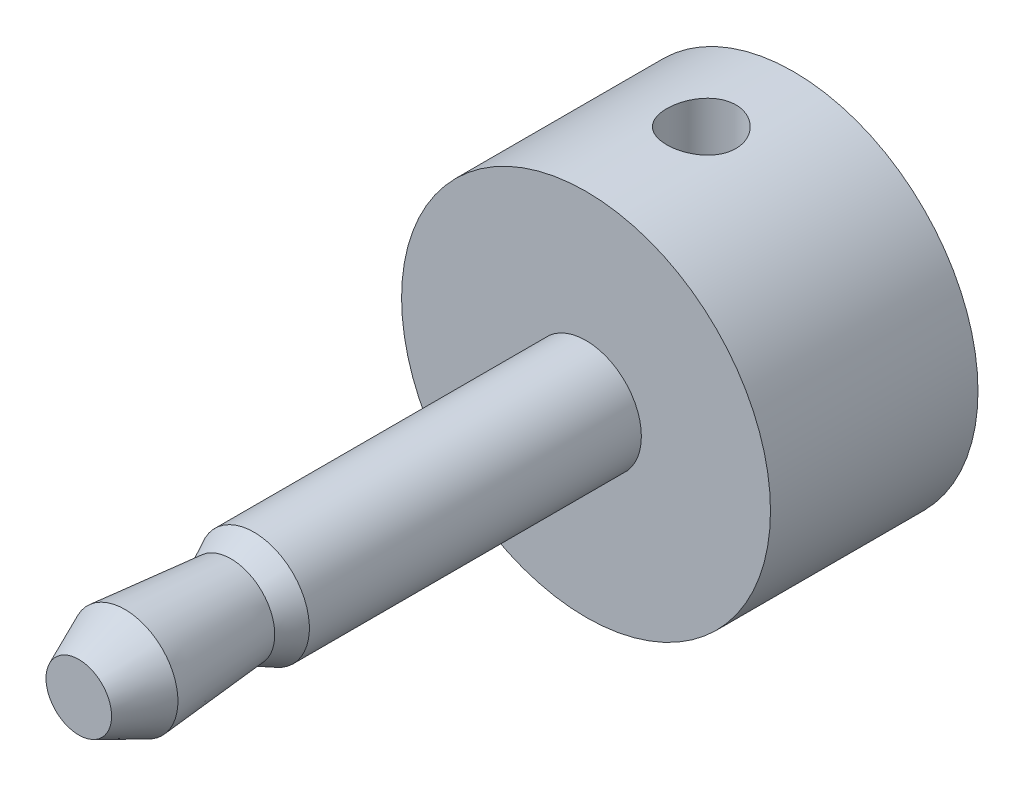
SolidWorks part; units mm, degrees
ref_plane "正面" through (0, 0, 0) normal (0, 0, 1) x (1, 0, 0)
ref_plane "平面" through (0, 0, 0) normal (0, 1, 0) x (1, 0, 0)
ref_plane "右側面" through (0, 0, 0) normal (1, 0, 0) x (0, 0, -1)
sketch "ｽｹｯﾁ1" plane through (0, 0, 0) normal (0, 0, 1) x (1, 0, 0)
  circle A0 centre (0, 0) radius 4
extrude "ﾎﾞｽ - 押し出し1" add sketch "ｽｹｯﾁ1" along normal blind 5.5
sketch "ｽｹｯﾁ2" plane through (0, 0, 5.5) normal (0, 0, 1) x (1, 0, 0)
  circle A0 centre (0, 0) radius 1.2
extrude "ﾎﾞｽ - 押し出し2" add sketch "ｽｹｯﾁ2" along normal blind 11
sketch "ｽｹｯﾁ3" plane through (0, 0, 16.5) normal (0, 0, 1) x (1, 0, 0)
  circle A0 centre (0, 0) radius 1.2 construction
  circle A1 centre (0, 0) radius 1.2 construction
  point P0 (-1.2, 0)
  point P1 (1.2, 0)
ref_plane "平面1" through (0, 0, 0) normal (0, 1, 0) x (1, 0, 0)
sketch "ｽｹｯﾁ4" plane through (0, 0, 0) normal (0, 1, 0) x (1, 0, 0)
  line L0 (1.2, -16.5) -> (0.7112, -16.5)
  line L5 (-1.2, -16.5) -> (1.2, -16.5) construction
  line L6 (0.7112, -16.5) -> (1.15, -15.5)
  line L7 (1.15, -15.5) -> (0.95, -13.2)
  line L8 (0.95, -13.2) -> (1.2, -12.7)
  line L9 (1.2, -16.5) -> (1.2, -5.5) construction
  line L10 (1.2, -12.7) -> (1.2, -16.5)
  point P12 (0, -16.5)
  dimension "D1" = 1
  dimension "D2" = 1.15
  dimension "D3" = 2.3
  dimension "D4" = 0.5
  dimension "D5" = 0.95
ref_axis "軸1" through (0, 0, 12.793) along (0, 0, 1)
revolve "ｶｯﾄ - 回転1" cut sketch "ｽｹｯﾁ4" angle 360 about axis through (0, 0, 12.793) along (0, 0, 1)
sketch "ｽｹｯﾁ6" plane through (0, 0, 0) normal (0, 1, 0) x (1, 0, 0)
  line L0 (4, 0) -> (-4, 0) construction
  circle A0 centre (0, -3) radius 0.75
  dimension "D1" = 3
extrude "ｶｯﾄ - 押し出し1" cut sketch "ｽｹｯﾁ6" against normal through all and the other way through all
sketch "ｽｹｯﾁ7" plane through (0, 0, 0) normal (0, 0, -1) x (-1, 0, 0)
  circle A0 centre (0, 0) radius 4
extrude "ｶｯﾄ - 押し出し2" cut sketch "ｽｹｯﾁ7" against normal blind 1
